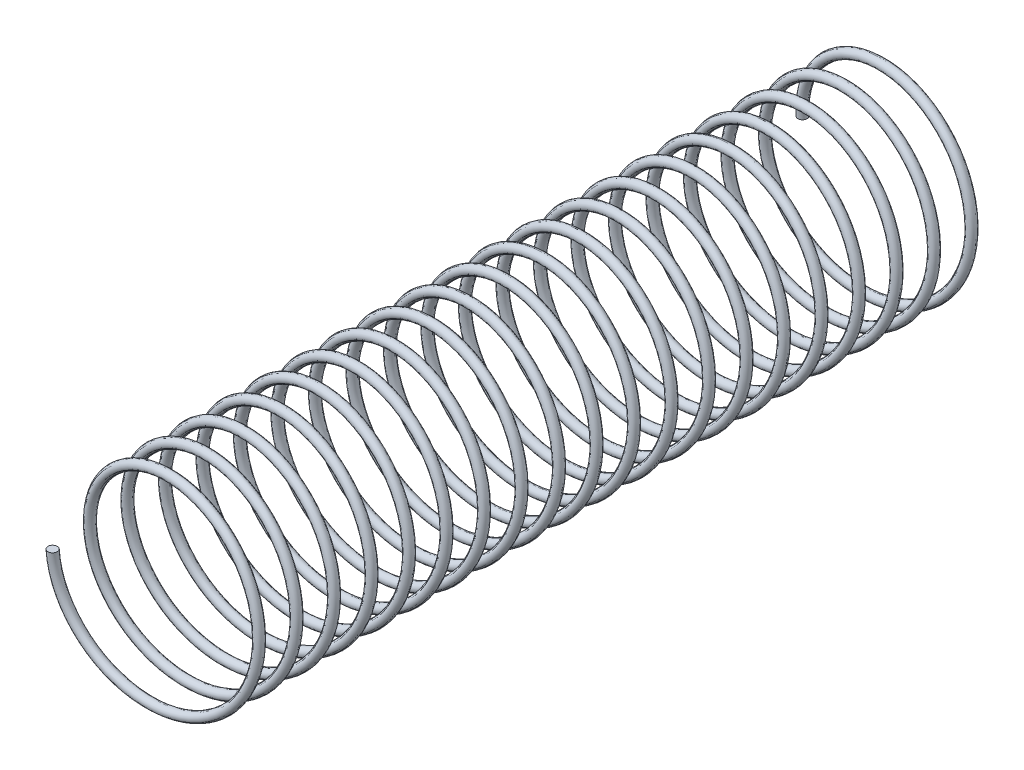
SolidWorks part; units mm, degrees
ref_plane "Front Plane" through (0, 0, 0) normal (0, 0, 1) x (1, 0, 0)
ref_plane "Top Plane" through (0, 0, 0) normal (0, 1, 0) x (1, 0, 0)
ref_plane "Right Plane" through (0, 0, 0) normal (1, 0, 0) x (0, 0, -1)
sketch "Sketch1" plane through (0, 0, 0) normal (0, 0, 1) x (1, 0, 0)
  circle A0 centre (0, 0) radius 3.175
  dimension "D1" = 6.35
curve "Helix/Spiral1" pitch 1.27 height 25.4 turns 20
sketch "Sketch2" plane through (0, 0, 0) normal (0, 1, 0) x (1, 0, 0)
  circle A0 centre (-3.175, 0) radius 0.1588
  spline S0 degree 3 poles (-3.175, 0) (-3.175, -0.0263) (-3.0097, -0.0795) (-2.3035, -0.1587) (-1.2467, -0.2381) (0, -0.3175) (1.2467, -0.3969) (2.3035, -0.4762) (3.0097, -0.5556) (3.2577, -0.635) (3.0097, -0.7144) (2.3035, -0.7937) (0.8944, -0.8996) (-0.8944, -1.0054) (-2.3035, -1.1112) (-3.0097, -1.1906) (-3.2577, -1.27) (-3.0097, -1.3494) (-2.3035, -1.4287) (-0.8944, -1.5346) (0.8944, -1.6404) (2.3035, -1.7462) (3.0097, -1.8256) (3.2577, -1.905) (3.0097, -1.9844) (2.3035, -2.0637) (0.8944, -2.1696) (-0.8944, -2.2754) (-2.3035, -2.3812) (-3.0097, -2.4606) (-3.2577, -2.54) (-3.0097, -2.6194) (-2.3035, -2.6987) (-0.8944, -2.8046) (0.8944, -2.9104) (2.3035, -3.0163) (3.0097, -3.0956) (3.2577, -3.175) (3.0097, -3.2544) (2.3035, -3.3337) (0.8944, -3.4396) (-0.8944, -3.5454) (-2.3035, -3.6513) (-3.0097, -3.7306) (-3.2577, -3.81) (-3.0097, -3.8894) (-2.3035, -3.9687) (-0.8944, -4.0746) (0.8944, -4.1804) (2.3035, -4.2862) (3.0097, -4.3656) (3.2577, -4.445) (3.0097, -4.5244) (2.3035, -4.6037) (0.8944, -4.7096) (-0.8944, -4.8154) (-2.3035, -4.9212) (-3.0097, -5.0006) (-3.2577, -5.08) (-3.0097, -5.1594) (-2.3035, -5.2387) (-0.8944, -5.3446) (0.8944, -5.4504) (2.3035, -5.5562) (3.0097, -5.6356) (3.2577, -5.715) (3.0097, -5.7944) (2.3035, -5.8737) (0.8944, -5.9796) (-0.8944, -6.0854) (-2.3035, -6.1912) (-3.0097, -6.2706) (-3.2577, -6.35) (-3.0097, -6.4294) (-2.3035, -6.5087) (-0.8944, -6.6146) (0.8944, -6.7204) (2.3035, -6.8262) (3.0097, -6.9056) (3.2577, -6.985) (3.0097, -7.0644) (2.3035, -7.1437) (0.8944, -7.2496) (-0.8944, -7.3554) (-2.3035, -7.4612) (-3.0097, -7.5406) (-3.2577, -7.62) (-3.0097, -7.6994) (-2.3035, -7.7787) (-0.8944, -7.8846) (0.8944, -7.9904) (2.3035, -8.0962) (3.0097, -8.1756) (3.2577, -8.255) (3.0097, -8.3344) (2.3035, -8.4137) (0.8944, -8.5196) (-0.8944, -8.6254) (-2.3035, -8.7312) (-3.0097, -8.8106) (-3.2577, -8.89) (-3.0097, -8.9694) (-2.3035, -9.0487) (-0.8944, -9.1546) (0.8944, -9.2604) (2.3035, -9.3662) (3.0097, -9.4456) (3.2577, -9.525) (3.0097, -9.6044) (2.3035, -9.6837) (0.8944, -9.7896) (-0.8944, -9.8954) (-2.3035, -10.0012) (-3.0097, -10.0806) (-3.2577, -10.16) (-3.0097, -10.2394) (-2.3035, -10.3187) (-0.8944, -10.4246) (0.8944, -10.5304) (2.3035, -10.6362) (3.0097, -10.7156) (3.2577, -10.795) (3.0097, -10.8744) (2.3035, -10.9537) (0.8944, -11.0596) (-0.8944, -11.1654) (-2.3035, -11.2712) (-3.0097, -11.3506) (-3.2577, -11.43) (-3.0097, -11.5094) (-2.3035, -11.5887) (-0.8944, -11.6946) (0.8944, -11.8004) (2.3035, -11.9062) (3.0097, -11.9856) (3.2577, -12.065) (3.0097, -12.1444) (2.3035, -12.2237) (0.8944, -12.3296) (-0.8944, -12.4354) (-2.3035, -12.5412) (-3.0097, -12.6206) (-3.2577, -12.7) (-3.0097, -12.7794) (-2.3035, -12.8587) (-0.8944, -12.9646) (0.8944, -13.0704) (2.3035, -13.1762) (3.0097, -13.2556) (3.2577, -13.335) (3.0097, -13.4144) (2.3035, -13.4937) (0.8944, -13.5996) (-0.8944, -13.7054) (-2.3035, -13.8112) (-3.0097, -13.8906) (-3.2577, -13.97) (-3.0097, -14.0494) (-2.3035, -14.1287) (-0.8944, -14.2346) (0.8944, -14.3404) (2.3035, -14.4462) (3.0097, -14.5256) (3.2577, -14.605) (3.0097, -14.6844) (2.3035, -14.7637) (0.8944, -14.8696) (-0.8944, -14.9754) (-2.3035, -15.0812) (-3.0097, -15.1606) (-3.2577, -15.24) (-3.0097, -15.3194) (-2.3035, -15.3987) (-0.8944, -15.5046) (0.8944, -15.6104) (2.3035, -15.7162) (3.0097, -15.7956) (3.2577, -15.875) (3.0097, -15.9544) (2.3035, -16.0337) (0.8944, -16.1396) (-0.8944, -16.2454) (-2.3035, -16.3512) (-3.0097, -16.4306) (-3.2577, -16.51) (-3.0097, -16.5894) (-2.3035, -16.6687) (-0.8944, -16.7746) (0.8944, -16.8804) (2.3035, -16.9862) (3.0097, -17.0656) (3.2577, -17.145) (3.0097, -17.2244) (2.3035, -17.3037) (0.8944, -17.4096) (-0.8944, -17.5154) (-2.3035, -17.6212) (-3.0097, -17.7006) (-3.2577, -17.78) (-3.0097, -17.8594) (-2.3035, -17.9387) (-0.8944, -18.0446) (0.8944, -18.1504) (2.3035, -18.2562) (3.0097, -18.3356) (3.2577, -18.415) (3.0097, -18.4944) (2.3035, -18.5737) (0.8944, -18.6796) (-0.8944, -18.7854) (-2.3035, -18.8912) (-3.0097, -18.9706) (-3.2577, -19.05) (-3.0097, -19.1294) (-2.3035, -19.2087) (-0.8944, -19.3146) (0.8944, -19.4204) (2.3035, -19.5262) (3.0097, -19.6056) (3.2577, -19.685) (3.0097, -19.7644) (2.3035, -19.8437) (0.8944, -19.9496) (-0.8944, -20.0554) (-2.3035, -20.1612) (-3.0097, -20.2406) (-3.2577, -20.32) (-3.0097, -20.3994) (-2.3035, -20.4787) (-0.8944, -20.5846) (0.8944, -20.6904) (2.3035, -20.7962) (3.0097, -20.8756) (3.2577, -20.955) (3.0097, -21.0344) (2.3035, -21.1137) (0.8944, -21.2196) (-0.8944, -21.3254) (-2.3035, -21.4312) (-3.0097, -21.5106) (-3.2577, -21.59) (-3.0097, -21.6694) (-2.3035, -21.7487) (-0.8944, -21.8546) (0.8944, -21.9604) (2.3035, -22.0662) (3.0097, -22.1456) (3.2577, -22.225) (3.0097, -22.3044) (2.3035, -22.3837) (0.8944, -22.4896) (-0.8944, -22.5954) (-2.3035, -22.7012) (-3.0097, -22.7806) (-3.2577, -22.86) (-3.0097, -22.9394) (-2.3035, -23.0187) (-0.8944, -23.1246) (0.8944, -23.2304) (2.3035, -23.3362) (3.0097, -23.4156) (3.2577, -23.495) (3.0097, -23.5744) (2.3035, -23.6537) (0.8944, -23.7596) (-0.8944, -23.8654) (-2.3035, -23.9712) (-3.0097, -24.0506) (-3.2577, -24.13) (-3.0097, -24.2094) (-2.3035, -24.2888) (-0.8944, -24.3946) (0.8944, -24.5004) (2.3035, -24.6063) (3.0097, -24.6856) (3.2577, -24.765) (3.0097, -24.8444) (2.3035, -24.9238) (1.2467, -25.0031) (0, -25.0825) (-1.2467, -25.1619) (-2.3035, -25.2413) (-3.0097, -25.3205) (-3.175, -25.3737) (-3.175, -25.4) knots 0 0 0 0 0.003125 0.00625 0.009375 0.0125 0.015625 0.01875 0.021875 0.025 0.028125 0.03125 0.034375 0.040625 0.04375 0.046875 0.05 0.053125 0.05625 0.059375 0.065625 0.06875 0.071875 0.075 0.078125 0.08125 0.084375 0.090625 0.09375 0.096875 0.1 0.103125 0.10625 0.109375 0.115625 0.11875 0.121875 0.125 0.128125 0.13125 0.134375 0.140625 0.14375 0.146875 0.15 0.153125 0.15625 0.159375 0.165625 0.16875 0.171875 0.175 0.178125 0.18125 0.184375 0.190625 0.19375 0.196875 0.2 0.203125 0.20625 0.209375 0.215625 0.21875 0.221875 0.225 0.228125 0.23125 0.234375 0.240625 0.24375 0.246875 0.25 0.253125 0.25625 0.259375 0.265625 0.26875 0.271875 0.275 0.278125 0.28125 0.284375 0.290625 0.29375 0.296875 0.3 0.303125 0.30625 0.309375 0.315625 0.31875 0.321875 0.325 0.328125 0.33125 0.334375 0.340625 0.34375 0.346875 0.35 0.353125 0.35625 0.359375 0.365625 0.36875 0.371875 0.375 0.378125 0.38125 0.384375 0.390625 0.39375 0.396875 0.4 0.403125 0.40625 0.409375 0.415625 0.41875 0.421875 0.425 0.428125 0.43125 0.434375 0.440625 0.44375 0.446875 0.45 0.453125 0.45625 0.459375 0.465625 0.46875 0.471875 0.475 0.478125 0.48125 0.484375 0.490625 0.49375 0.496875 0.5 0.503125 0.50625 0.509375 0.515625 0.51875 0.521875 0.525 0.528125 0.53125 0.534375 0.540625 0.54375 0.546875 0.55 0.553125 0.55625 0.559375 0.565625 0.56875 0.571875 0.575 0.578125 0.58125 0.584375 0.590625 0.59375 0.596875 0.6 0.603125 0.60625 0.609375 0.615625 0.61875 0.621875 0.625 0.628125 0.63125 0.634375 0.640625 0.64375 0.646875 0.65 0.653125 0.65625 0.659375 0.665625 0.66875 0.671875 0.675 0.678125 0.68125 0.684375 0.690625 0.69375 0.696875 0.7 0.703125 0.70625 0.709375 0.715625 0.71875 0.721875 0.725 0.728125 0.73125 0.734375 0.740625 0.74375 0.746875 0.75 0.753125 0.75625 0.759375 0.765625 0.76875 0.771875 0.775 0.778125 0.78125 0.784375 0.790625 0.79375 0.796875 0.8 0.803125 0.80625 0.809375 0.815625 0.81875 0.821875 0.825 0.828125 0.83125 0.834375 0.840625 0.84375 0.846875 0.85 0.853125 0.85625 0.859375 0.865625 0.86875 0.871875 0.875 0.878125 0.88125 0.884375 0.890625 0.89375 0.896875 0.9 0.903125 0.90625 0.909375 0.915625 0.91875 0.921875 0.925 0.928125 0.93125 0.934375 0.940625 0.94375 0.946875 0.95 0.953125 0.95625 0.959375 0.965625 0.96875 0.971875 0.975 0.978125 0.98125 0.984375 0.9875 0.990625 0.99375 0.996875 1 1 1 1 construction
  dimension "D1" = 0.3175
sweep "Sweep1" add profiles "Sketch2" path "Helix/Spiral1"
